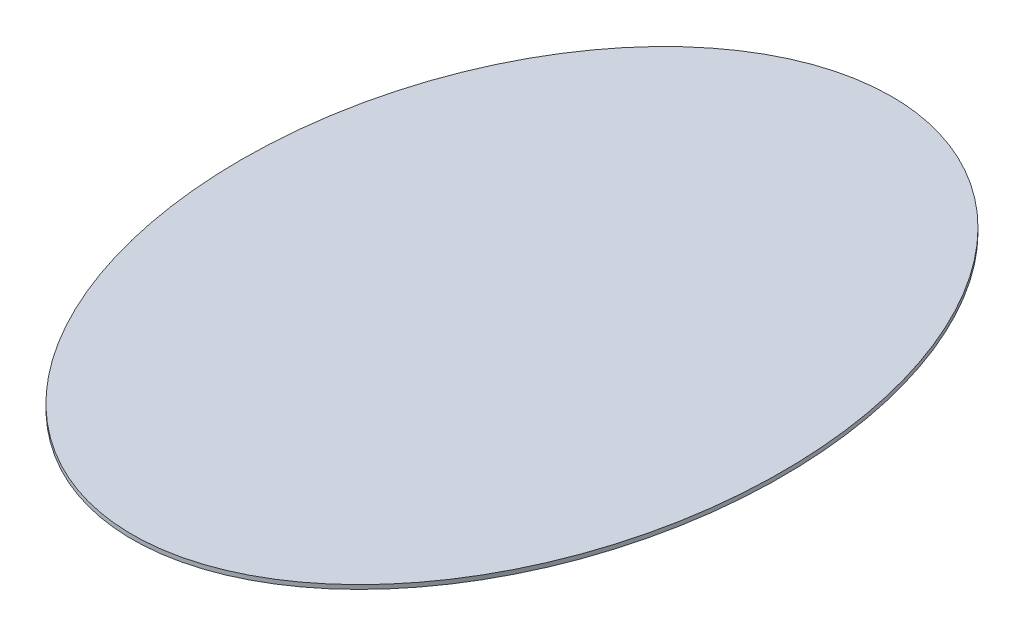
SolidWorks part; units mm, degrees
ref_plane "Front Plane" through (0, 0, 0) normal (0, 0, 1) x (1, 0, 0)
ref_plane "Top Plane" through (0, 0, 0) normal (0, 1, 0) x (1, 0, 0)
ref_plane "Right Plane" through (0, 0, 0) normal (1, 0, 0) x (0, 0, -1)
sketch "Sketch1" plane through (0, 0, 0) normal (0, 1, 0) x (1, 0, 0)
  ellipse E0 centre (0, 0) end of major axis (0, 355) minor radius 250 construction
  ellipse E1 centre (0, 0) end of major axis (0, 365) minor radius 260
  dimension "D1" = 500
  dimension "D2" = 710
  dimension "D3" = 520
  dimension "D4" = 730
extrude "Boss-Extrude1" add sketch "Sketch1" along normal blind 4
